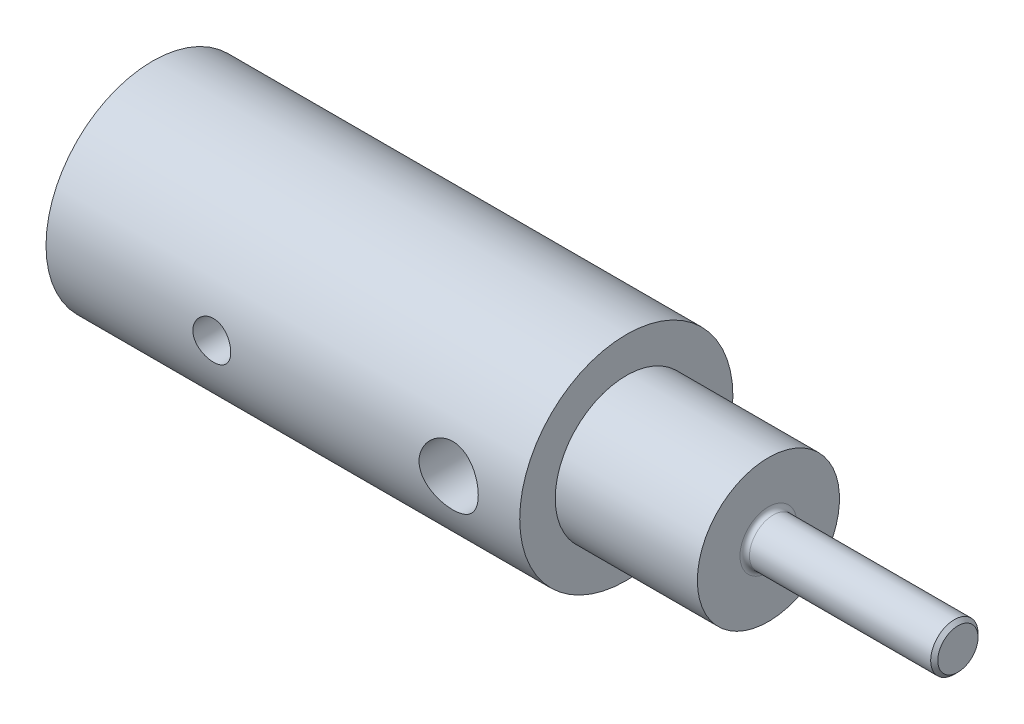
SolidWorks part; units mm, degrees
material "1.4301 (X5CrNi18-10)"
ref_plane "Vorne" through (0, 0, 0) normal (0, 0, 1) x (1, 0, 0)
ref_plane "Oben" through (0, 0, 0) normal (0, 1, 0) x (1, 0, 0)
ref_plane "Rechts" through (0, 0, 0) normal (1, 0, 0) x (0, 0, -1)
sketch "Skizze1" plane through (0, 0, 0) normal (0, 0, 1) x (1, 0, 0)
  line L0 (0, 0) -> (71.7919, 0) construction
  line L1 (0, 4.5) -> (0, 2)
  line L2 (0, 2) -> (14, 2)
  line L3 (14, 2) -> (15.2017, 0)
  line L4 (15.2017, 0) -> (34, 0)
  line L5 (26, 1) -> (26, 3)
  line L6 (26, 3) -> (20, 3)
  line L7 (20, 3) -> (20, 4.5)
  line L8 (20, 4.5) -> (0, 4.5)
  line L9 (26, 1) -> (34, 1)
  line L10 (34, 1) -> (34, 0)
  dimension "D1" = 4
  dimension "D2" = 6
  dimension "D3" = 6
  dimension "D4" = 59
  dimension "D5" = 14
  dimension "D6" = 9
  dimension "D7" = 20
  dimension "D8" = 8
  dimension "D9" = 2
revolve "Rotation1" add sketch "Skizze1" angle 360 about L0
cosmetic thread "Gewindedarstellung3" parameters "D1"=7.2, "D2"=1.548
ref_plane "Ebene1" through (0, 0, -4.5) normal (0, 0, -1) x (-1, 0, 0)
chamfer "Fase1" distance 0.15 angle 45 1 edges at (34, 0, 1)
sketch "Skizze2" plane through (0, 0, 0) normal (0, 0, 1) x (1, 0, 0)
  line L0 (26, 1.25) -> (27, 1.25)
  line L1 (26, 1.25) -> (26, 0.75)
  line L2 (27, 1.25) -> (27, 0.75)
  line L3 (26, 0.75) -> (27, 0.75)
  line L4 (26, -3) -> (26, 3) construction
  line L5 (0, 0) -> (35.0484, 0) construction
  dimension "D1" = 1.5
  dimension "D2" = 0.5
  dimension "D3" = 1
hole_wizard "M2 Gewindebohrung1" positions "Skizze6" profile "Skizze5" tap size "M2" standard "Iso"
sketch "Skizze6" plane through (0, 0, 0) normal (0, 0, 1) x (1, 0, 0)
  point P0 (7, 0)
  dimension "D1" = 7
sketch "Skizze5" plane through (7, 0, 0) normal (1, 0, 0) x (0, 1, 0)
  line L0 (0, 0) -> (0, 4.5)
  line L1 (0, 4.5) -> (0.8, 4.5)
  line L2 (0.8, 4.5) -> (0.8, 0)
  line L5 (0.8, 0) -> (0, 0)
  line L11 (0, -6.35) -> (0, 107.95) construction
  dimension "Nenndurchmesser (Haupt)" = 1.6
  dimension "Bohrungstiefe" = 4.5
cosmetic thread "Gewindedarstellung2" parameters "D2"=2
sketch "Skizze7" plane through (0, 0, 0) normal (0, 0, 1) x (1, 0, 0)
  circle A0 centre (17, 0) radius 1.25
  dimension "D1" = 2.5
  dimension "D2" = 17
extrude "Schnitt-Linear austragen2" cut sketch "Skizze7" against normal through all and the other way through all
fillet "Verrundung1" radius 0.2 1 edges at (26, 0, 1)
move or copy body "Körper-Verschieben/Kopieren1" [suppressed] bodies to move or copy 107
